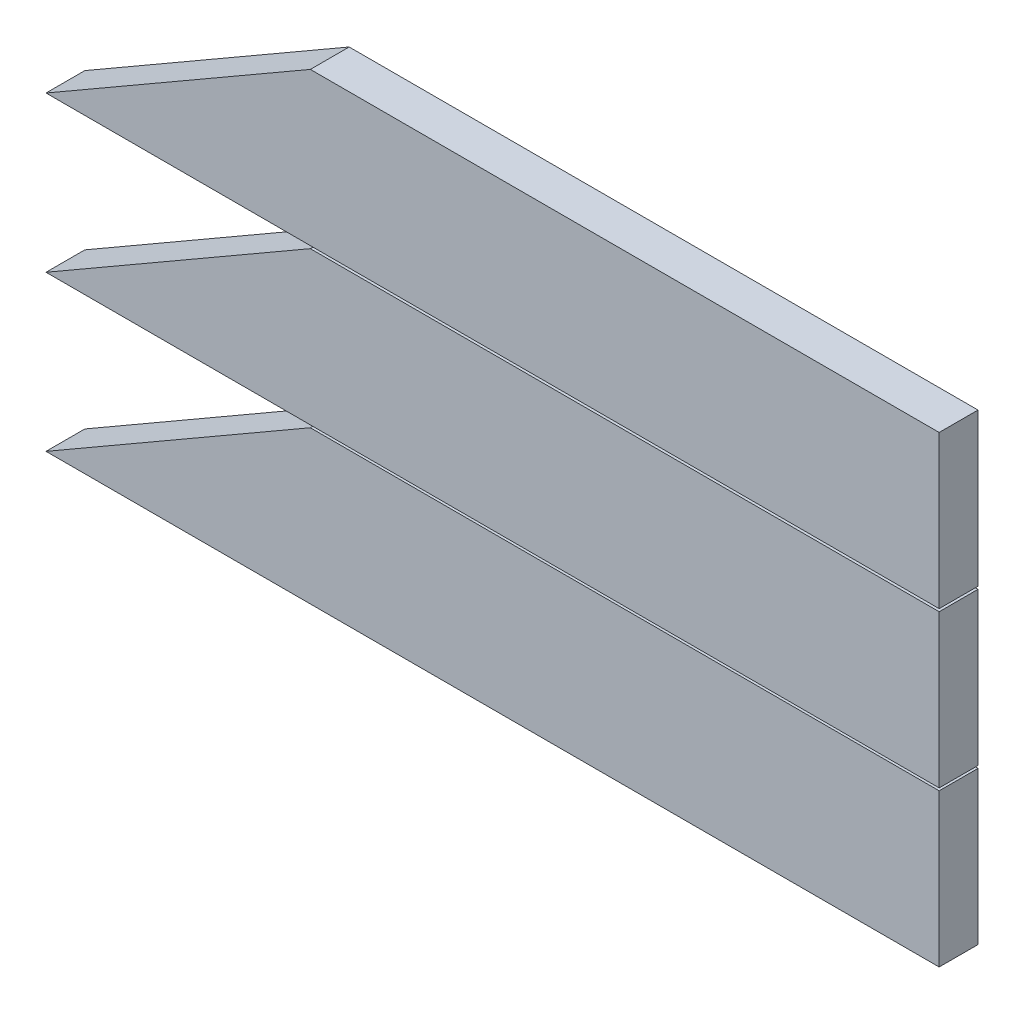
SolidWorks part; units mm, degrees
ref_plane "Front Plane" through (0, 0, 0) normal (0, 0, 1) x (1, 0, 0)
ref_plane "Top Plane" through (0, 0, 0) normal (0, 1, 0) x (1, 0, 0)
ref_plane "Right Plane" through (0, 0, 0) normal (1, 0, 0) x (0, 0, -1)
sketch "Sketch1" plane through (0, 0, 0) normal (0, 0, 1) x (1, 0, 0)
  line L0 (0, 0) -> (-411.3032, 0)
  line L1 (-411.3032, 0) -> (-584.2, -99.822)
  line L2 (-584.2, -99.822) -> (0, -99.822)
  line L3 (0, -99.822) -> (0, 0)
  line L4 (0, 101.5397) -> (-411.3032, 101.5397)
  line L5 (-411.3032, 101.5397) -> (-584.2, 1.7177)
  line L6 (-584.2, 1.7177) -> (0, 1.7177)
  line L7 (0, 1.7177) -> (0, 101.5397)
  line L12 (0, -101.4458) -> (-411.3032, -101.4458)
  line L13 (-411.3032, -101.4458) -> (-584.2, -201.2678)
  line L14 (-584.2, -201.2678) -> (0, -201.2678)
  line L15 (0, -201.2678) -> (0, -101.4458)
  dimension "D1" = 30
  dimension "D2" = 584.2
  dimension "D3" = 99.822
extrude "Boss-Extrude1" add sketch "Sketch1" along normal blind 25.4
